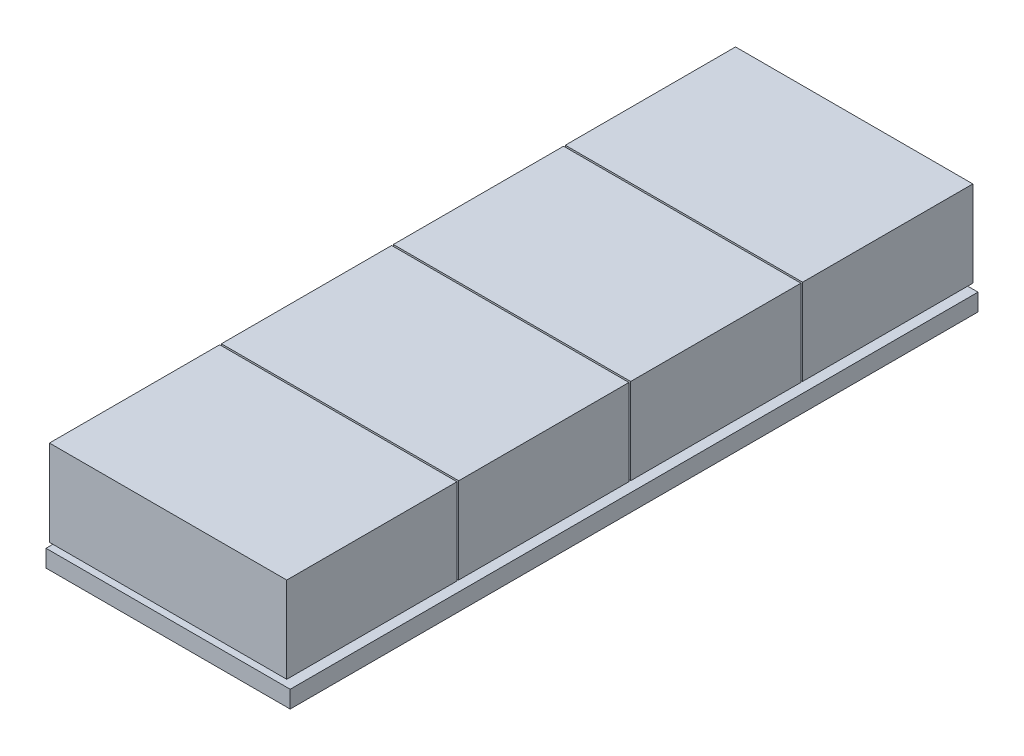
SolidWorks part; units mm, degrees
ref_plane "Front Plane" through (0, 0, 0) normal (0, 0, 1) x (1, 0, 0)
ref_plane "Top Plane" through (0, 0, 0) normal (0, 1, 0) x (1, 0, 0)
ref_plane "Right Plane" through (0, 0, 0) normal (1, 0, 0) x (0, 0, -1)
sketch "Sketch1" plane through (0, 0, 0) normal (0, 1, 0) x (1, 0, 0)
  line L1 (-35.5, -100) -> (35.5, -100)
  line L2 (-35.5, -100) -> (-35.5, 100)
  line L3 (-35.5, 100) -> (35.5, 100)
  line L4 (35.5, -100) -> (35.5, 100)
  line L5 (-35.5, -100) -> (35.5, 100) construction
  line L6 (-35.5, 100) -> (35.5, -100) construction
  point P0 (0, 0)
  dimension "D1" = 71
  dimension "D2" = 200
extrude "Boss-Extrude1" add sketch "Sketch1" along normal blind 5
sketch "Sketch2" plane through (0, 5, 0) normal (0, 1, 0) x (1, 0, 0)
  line L0 (0, 0) -> (0, -100) construction
  line L1 (-35.5, -100) -> (35.5, -100) construction
  line L3 (-32.5, -52.5) -> (32.5, -52.5)
  line L4 (-32.5, -52.5) -> (-32.5, -97.5)
  line L5 (-32.5, -97.5) -> (32.5, -97.5)
  line L6 (32.5, -52.5) -> (32.5, -97.5)
  line L7 (-32.5, -52.5) -> (32.5, -97.5) construction
  line L8 (-32.5, -97.5) -> (32.5, -52.5) construction
  point P5 (0, -75)
  dimension "D1" = 65
  dimension "D2" = 45
  dimension "D3" = 2.5
extrude "Boss-Extrude3" add sketch "Sketch2" along normal blind 2
pattern_linear "LPattern1" count 4 spacing 50 along (0, 0, -1) of "Boss-Extrude3"
sketch "Sketch3" plane through (0, 7, 0) normal (0, 1, 0) x (1, 0, 0)
  line L0 (0, 0) -> (0, -97.5) construction
  line L1 (-32.5, -97.5) -> (32.5, -97.5) construction
  line L2 (-35.5, 100) -> (-35.5, -100) construction
  line L3 (-34.5, -50.5) -> (34.5, -50.5)
  line L4 (-34.5, -50.5) -> (-34.5, -100)
  line L5 (-34.5, -100) -> (34.5, -100)
  line L6 (34.5, -50.5) -> (34.5, -100)
  line L7 (-34.5, -50.5) -> (34.5, -100) construction
  line L8 (-34.5, -100) -> (34.5, -50.5) construction
  line L9 (-32.5, -47.5) -> (32.5, -47.5) construction
  dimension "D1" = 1
  dimension "D2" = 49.5
  dimension "D3" = 3
extrude "Boss-Extrude8" add sketch "Sketch3" along normal blind 25
pattern_linear "LPattern5" count 4 spacing 50 along (0, 0, -1) of "Boss-Extrude8"
